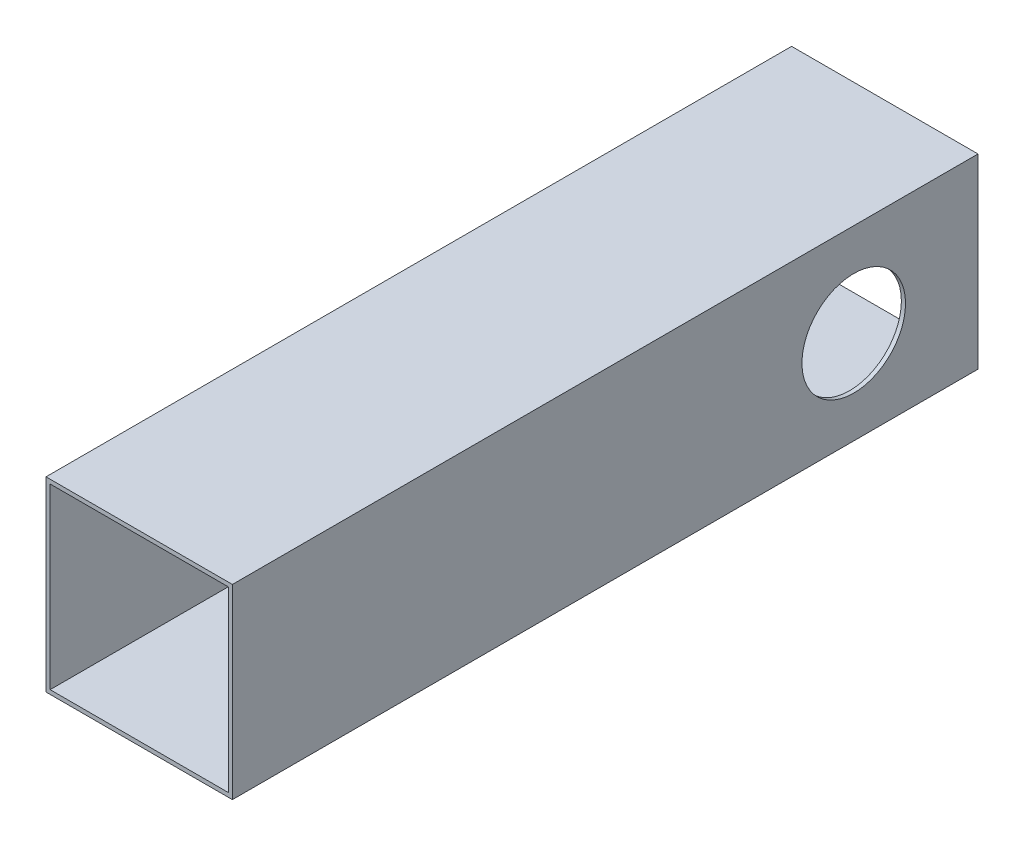
SolidWorks part; units mm, degrees
ref_plane "Front Plane" through (0, 0, 0) normal (0, 0, 1) x (1, 0, 0)
ref_plane "Top Plane" through (0, 0, 0) normal (0, 1, 0) x (1, 0, 0)
ref_plane "Right Plane" through (0, 0, 0) normal (1, 0, 0) x (0, 0, -1)
sketch "Sketch1" plane through (0, 0, 0) normal (0, 0, 1) x (1, 0, 0)
  line L1 (-22.5, -22.5) -> (22.5, -22.5)
  line L2 (-22.5, -22.5) -> (-22.5, 22.5)
  line L3 (-22.5, 22.5) -> (22.5, 22.5)
  line L4 (22.5, -22.5) -> (22.5, 22.5)
  line L5 (-22.5, -22.5) -> (22.5, 22.5) construction
  line L6 (-22.5, 22.5) -> (22.5, -22.5) construction
  line L7 (-21.5, -21.5) -> (21.5, -21.5)
  line L8 (-21.5, -21.5) -> (-21.5, 21.5)
  line L9 (-21.5, 21.5) -> (21.5, 21.5)
  line L10 (21.5, -21.5) -> (21.5, 21.5)
  line L11 (-21.5, -21.5) -> (21.5, 21.5) construction
  line L12 (-21.5, 21.5) -> (21.5, -21.5) construction
  point P0 (0, 0)
  point P6 (0, 0)
  dimension "D1" = 45
  dimension "D2" = 45
  dimension "D3" = 1
  dimension "D4" = 1
extrude "Boss-Extrude1" add sketch "Sketch1" along normal blind 180
sketch "Sketch2" plane through (22.5, 0, 0) normal (1, 0, 0) x (0, 0, -1)
  line L0 (0, 0) -> (-180, 0) construction
  line L1 (-180, -22.5) -> (-180, 22.5) construction
  line L2 (0, -22.5) -> (0, 22.5) construction
  circle A0 centre (-30, 0) radius 12.5
  dimension "D1" = 25
  dimension "D2" = 30
extrude "Cut-Extrude1" cut sketch "Sketch2" against normal blind 180
